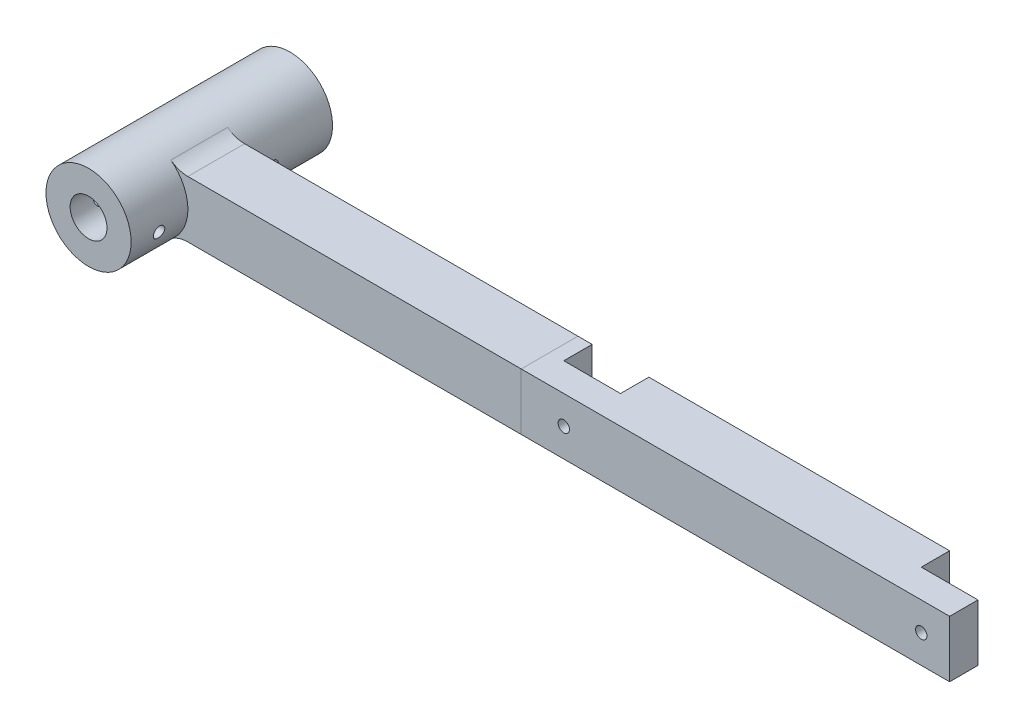
SolidWorks part; units mm, degrees
ref_plane "Front Plane" through (0, 0, 0) normal (0, 0, 1) x (1, 0, 0)
ref_plane "Top Plane" through (0, 0, 0) normal (0, 1, 0) x (1, 0, 0)
ref_plane "Right Plane" through (0, 0, 0) normal (1, 0, 0) x (0, 0, -1)
sketch "Sketch1" plane through (0, 0, 0) normal (0, 0, 1) x (1, 0, 0)
  line L0 (-130, 10) -> (0, 10) construction
  line L1 (0, 0) -> (-130, 0) construction
  line L2 (0, 0) -> (0, 20)
  line L3 (0, 20) -> (-130, 20) construction
  line L4 (-130, 0) -> (-130, 20) construction
  line L5 (-130, 20) -> (-137.5, 20) construction
  line L6 (-122.5, 20) -> (0, 20)
  line L7 (0, 0) -> (-122.5, 0)
  circle A0 centre (-137.5, 10) radius 6.55
  arc A1 (-128.5, 22) -> (-128.5, -2) centre (-137.5, 10) ccw
  arc A2 (-128.5, -2) -> (-122.5, 0) centre (-122.5, -10) cw
  arc A3 (-128.5, 22) -> (-122.5, 20) centre (-122.5, 30) ccw
  point P14 (-126.3197, 0)
  point P17 (-126.3197, 20)
  dimension "D4" = 13.1
  dimension "D5" = 15
  dimension "D6" = 10
  dimension "D1" = 130
  dimension "D2" = 20
  dimension "D3" = 7.5
extrude "Boss-Extrude1" add sketch "Sketch1" along normal blind 20
sketch "Sketch2" plane through (0, 0, 0) normal (0, 0, -1) x (-1, 0, 0)
  circle A0 centre (137.5, 10) radius 6.5
  circle A1 centre (137.5, 10) radius 15
extrude "Boss-Extrude2" add sketch "Sketch2" along normal blind 31
sketch "Sketch3" plane through (0, 0, 20) normal (0, 0, 1) x (1, 0, 0)
  circle A0 centre (-137.5, 10) radius 6.5
  circle A1 centre (-137.5, 10) radius 15
extrude "Boss-Extrude3" add sketch "Sketch3" along normal blind 20
sketch "Sketch4" plane through (0, 0, 20) normal (0, 0, 1) x (1, 0, 0)
  line L1 (0, 0) -> (146, 0)
  line L2 (0, 0) -> (0, 20)
  line L3 (0, 20) -> (146, 20)
  line L4 (146, 0) -> (146, 20)
  dimension "D1" = 146
  dimension "D2" = 20
extrude "Boss-Extrude4" add sketch "Sketch4" against normal up to surface (20 mm away) up to face at (-82.7208, 10, 0)
sketch "Sketch7" plane through (0, 20, 0) normal (0, 1, 0) x (1, 0, 0)
  line L0 (146, 0) -> (-122.5, 0) construction
  line L1 (146, 0) -> (126, 0)
  line L2 (146, 0) -> (146, -10)
  line L3 (146, -10) -> (126, -10)
  line L4 (126, 0) -> (126, -10)
  line L5 (20, 0) -> (0, 0)
  line L6 (20, 0) -> (20, -10)
  line L7 (20, -10) -> (0, -10)
  line L8 (0, 0) -> (0, -10)
  line L9 (146, 0) -> (146, -20) construction
  dimension "D1" = 20
  dimension "D2" = 10
  dimension "D3" = 20
  dimension "D4" = 10
  dimension "D5" = 106
extrude "Cut-Extrude1" cut sketch "Sketch7" against normal up to surface (20 mm away) up to face at (11.75, 0, 10)
sketch "Sketch8" plane through (0, 0, 10) normal (0, 0, -1) x (-1, 0, 0)
  circle A0 centre (-136, 10) radius 2
  circle A1 centre (-10, 10) radius 2
  dimension "D1" = 4
  dimension "D2" = 4
extrude "Cut-Extrude2" cut sketch "Sketch8" against normal up to surface (10 mm away) up to face at (-34.0541, 10, 20)
ref_plane "Plane1" through (-122.5, 0, 0) normal (1, 0, 0) x (0, 0, -1)
sketch "Sketch9" plane through (-122.5, 0, 0) normal (1, 0, 0) x (0, 0, -1)
  line L1 (-40, 25) -> (-40, -5) construction
  circle A0 centre (-30, 7.8865) radius 2
  circle A1 centre (10, 7.8865) radius 2
  dimension "D3" = 4
  dimension "D4" = 4
  dimension "D1" = 50
  dimension "D2" = 10
extrude "Cut-Extrude3" cut sketch "Sketch9" against normal through all
sketch "Sketch14" plane through (0, 20, 0) normal (0, 1, 0) x (1, 0, 0)
  line L0 (-5, 0) -> (-5, -20)
  line L1 (146, -20) -> (-122.5, -20) construction
  line L2 (0, 0) -> (0, -10) construction
  dimension "D1" = 5
split "Split1" trim tools "Sketch14" bodies to split 107 resulting bodies 112 113
